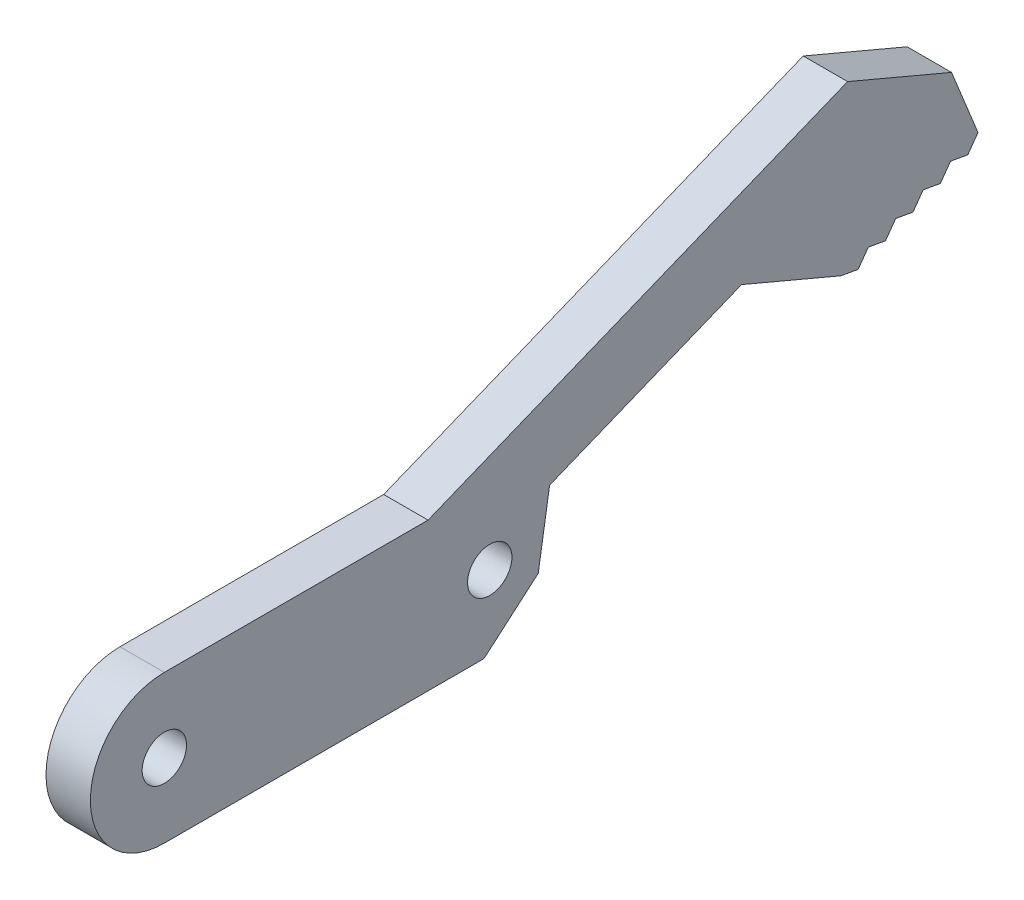
SolidWorks part; units mm, degrees
ref_plane "Front" through (0, 0, 0) normal (0, 0, 1) x (1, 0, 0)
ref_plane "Top" through (0, 0, 0) normal (0, 1, 0) x (1, 0, 0)
ref_plane "Right" through (0, 0, 0) normal (1, 0, 0) x (0, 0, -1)
sketch "Sketch1" plane through (0, 0, 0) normal (1, 0, 0) x (0, 0, -1)
  line L1 (-11, -5) -> (11, -5)
  line L2 (-11, -5) -> (-11, 5) construction
  line L3 (-11, 5) -> (11, 5)
  line L4 (11, -5) -> (11, 5) construction
  line L5 (-11, -5) -> (11, 5) construction
  line L6 (-11, 5) -> (11, -5) construction
  circle A0 centre (11, 0) radius 5
  circle A1 centre (-11, 0) radius 5
  circle A2 centre (11, 0) radius 1.5
  circle A3 centre (-11, 0) radius 1.5
  point P0 (0, 0)
  dimension "D1" = 10
  dimension "D2" = 3
  dimension "D3" = 3
  dimension "D4" = 22
extrude "Boss-Extrude1" add sketch "Sketch1" along normal mid plane 3 contours A1 L1 A0 L3 | A1 A3 | A0 A2
sketch "Sketch2" plane through (1.5, 0, 0) normal (1, 0, 0) x (0, 0, -1)
  line L0 (10.8825, -5) -> (44.248, 8.5185)
  line L2 (44.248, 8.5185) -> (40.1963, 18.5185)
  line L3 (6.8309, 5) -> (40.1963, 18.5185)
  line L4 (-11, -5) -> (11, -5) construction
  line L5 (-11, 5) -> (11, 5) construction
  line L6 (6.8309, 5) -> (11, 5)
  line L7 (11.8564, -4.6054) -> (15.0482, 2.9346)
  line L8 (15.0482, 2.9346) -> (28.0237, 8.1917)
  line L10 (34.9798, 4.7633) -> (34.7432, 5.3472)
  line L11 (34.7432, 5.3472) -> (28.0237, 8.1917)
  arc A0 (11, -5) -> (11, 5) centre (11, 0) ccw construction
  arc A1 (15.0482, 2.9346) -> (11, 5) centre (11, 0) ccw
  line M10 (11, 5) -> (-11, 5)
  arc M13 (11, -5) -> (11, 5) centre (11, 0) ccw
  dimension "D1" = 0.63
  dimension "D2" = 10
  dimension "D3" = 10
  dimension "D4" = 36
  dimension "D5" = 45
  dimension "D6" = 45
  dimension "D7" = 5
  dimension "D8" = 157.944
  dimension "D9" = 14
extrude "Boss-Extrude2" add sketch "Sketch2" against normal blind 3 contours L11 L10 L0 L2 L3 L8 M10 M13
sketch "Sketch3" plane through (1.5, 0, 0) normal (1, 0, 0) x (0, 0, -1)
  line L0 (40.1963, 18.5185) -> (35.1963, 16.4926)
  line L1 (6.8309, 5) -> (40.1963, 18.5185) construction
  line L2 (35.1963, 16.4926) -> (42.2221, 13.5185)
  line L3 (44.248, 8.5185) -> (40.1963, 18.5185) construction
  line L4 (42.2221, 13.5185) -> (40.1963, 18.5185)
  line L5 (34.7432, 5.3472) -> (28.0237, 8.1917) construction
extrude "Cut-Extrude1" cut sketch "Sketch3" against normal blind 3
sketch "Sketch4" plane through (1.5, 0, 0) normal (1, 0, 0) x (0, 0, -1)
  line L0 (15.0482, 2.9346) -> (14.2799, -1.8441)
  line L1 (14.2799, -1.8441) -> (10.6103, -5)
  line L2 (-11, -5) -> (11, -5) construction
  line L3 (10.6103, -5) -> (11, -5)
  line L4 (34.7432, 5.3472) -> (44.0114, 9.1023) construction
  line L5 (44.248, 8.5185) -> (42.2221, 13.5185) construction
  line L6 (34.9798, 4.7633) -> (44.248, 8.5185) construction
  line L7 (34.7432, 5.3472) -> (35.9066, 5.1388)
  line L8 (35.9066, 5.1388) -> (36.5968, 6.0982)
  line L9 (36.5968, 6.0982) -> (37.7602, 5.8899)
  line L10 (37.7602, 5.8899) -> (38.4505, 6.8493)
  line L11 (38.4505, 6.8493) -> (39.6139, 6.6409)
  line L12 (39.6139, 6.6409) -> (40.3041, 7.6003)
  line L13 (40.3041, 7.6003) -> (41.4675, 7.3919)
  line L14 (41.4675, 7.3919) -> (42.1577, 8.3513)
  line L15 (42.1577, 8.3513) -> (43.3211, 8.1429)
  line L16 (43.3211, 8.1429) -> (44.0114, 9.1023)
  line L17 (34.7432, 5.3472) -> (34.9798, 4.7633)
  line L18 (34.9798, 4.7633) -> (44.248, 8.5185)
  line L19 (44.248, 8.5185) -> (44.0114, 9.1023)
  arc A0 (11, -5) -> (15.0482, 2.9346) centre (11, 0) ccw construction
  arc A1 (11, -5) -> (15.0482, 2.9346) centre (11, 0) ccw
  line M13 (-11, -5) -> (11, -5)
  arc M14 (11, -5) -> (15.0482, 2.9346) centre (11, 0) ccw
  line M17 (34.7432, 5.3472) -> (34.9798, 4.7633)
  line M18 (34.9798, 4.7633) -> (44.248, 8.5185)
  line M19 (44.248, 8.5185) -> (42.2221, 13.5185)
  dimension "D1" = 4.84
extrude "Cut-Extrude2" cut sketch "Sketch4" against normal blind 3 contours L9 L8 M18 | L7 M17 M18 | L11 L10 M18 | L13 L12 M18 | L15 L14 M18 | L16 M18 M19 | L0 L1 M13 M14
